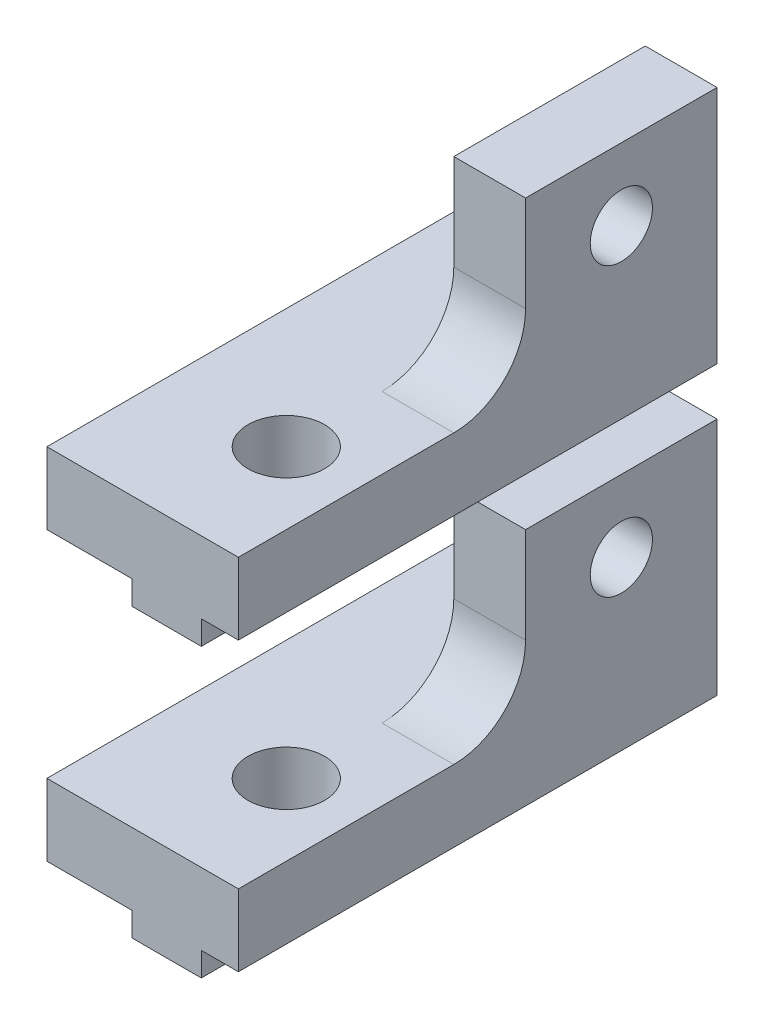
SolidWorks part; units mm, degrees
ref_plane "Front Plane" through (0, 0, 0) normal (0, 0, 1) x (1, 0, 0)
ref_plane "Top Plane" through (0, 0, 0) normal (0, 1, 0) x (1, 0, 0)
ref_plane "Right Plane" through (0, 0, 0) normal (1, 0, 0) x (0, 0, -1)
sketch "Esquisse1" plane through (0, 0, 0) normal (0, 0, 1) x (1, 0, 0)
  line L0 (0, 0) -> (8, 0)
  line L1 (8, 0) -> (8, 10)
  line L3 (5, 3) -> (5, 10)
  line L5 (5, 3) -> (0, 3)
  line L6 (0, 3) -> (0, 0)
  line L7 (5, 10) -> (8, 10)
  point P6 (7.5, 9.8103)
  point P9 (4.4239, 3)
  point P10 (0, 1.8222)
  dimension "D1" = 8
  dimension "D2" = 3
  dimension "D3" = 10
  dimension "D4" = 3
extrude "Main" add sketch "Esquisse1" along normal blind 20
sketch "Esquisse2" plane through (0, 0, 0) normal (-1, 0, 0) x (0, 0, 1)
  line L4 (0, 3) -> (0, 0) construction
  line L5 (20, 10) -> (0, 10) construction
  circle A0 centre (4, 7) radius 1.3
  point P2 (-2.4499, 0)
  point P3 (3.8612, 0)
  point P4 (4, 6.0529)
  dimension "D1" = 2.6
  dimension "D2" = 3
  dimension "D3" = 4
extrude "Vertical Hole" cut sketch "Esquisse2" against normal through all both and the other way through all
sketch "Esquisse6" plane through (5, 0, 0) normal (1, 0, 0) x (0, 0, -1)
  line L1 (-20, 10) -> (-8, 10)
  line L2 (-20, 10) -> (-20, 3)
  line L3 (-20, 3) -> (-8, 3)
  line L4 (-8, 10) -> (-8, 3)
  line L6 (-20, 10) -> (-20, 3) construction
  line L7 (-20, 10) -> (0, 10) construction
  line L8 (-20, 3) -> (0, 3) construction
  point P5 (-20, 10)
  point P10 (-8, 3)
  dimension "D1" = 12
extrude "Cut Borders" cut sketch "Esquisse6" along normal through all
sketch "Esquisse7" plane through (0, 0, 20) normal (0, 0, 1) x (1, 0, 0)
  line L0 (0, 0) -> (8, 0) construction
  line L1 (3.55, 0) -> (6.45, 0)
  line L2 (3.55, 0) -> (3.55, -1)
  line L3 (3.55, -1) -> (6.45, -1)
  line L4 (6.45, 0) -> (6.45, -1)
  line L5 (0, 3) -> (0, 0) construction
  dimension "D1" = 1
  dimension "D2" = 3.55
  dimension "D3" = 2.9
extrude "MakerBeamSupport" add sketch "Esquisse7" against normal up to surface (20 mm away) up to face at (4.3333, 4.3333, 0)
sketch "Esquisse3" plane through (0, 3, 0) normal (0, -1, 0) x (1, 0, 0)
  line L6 (8, 20) -> (5, 20) construction
  line L7 (0, 20) -> (0, 0) construction
  circle A1 centre (5, 15) radius 1.6
  dimension "D1" = 3.2
  dimension "D2" = 5
  dimension "D3" = 5
extrude "Horizontal Hole" cut sketch "Esquisse3" along normal blind 10 and the other way through all
fillet "Congé1" radius 3 1 edges at (6.5, 3, 8)
pattern_linear "LPattern1" count 2 spacing 12 along (0, 1, 0) of bodies 115
